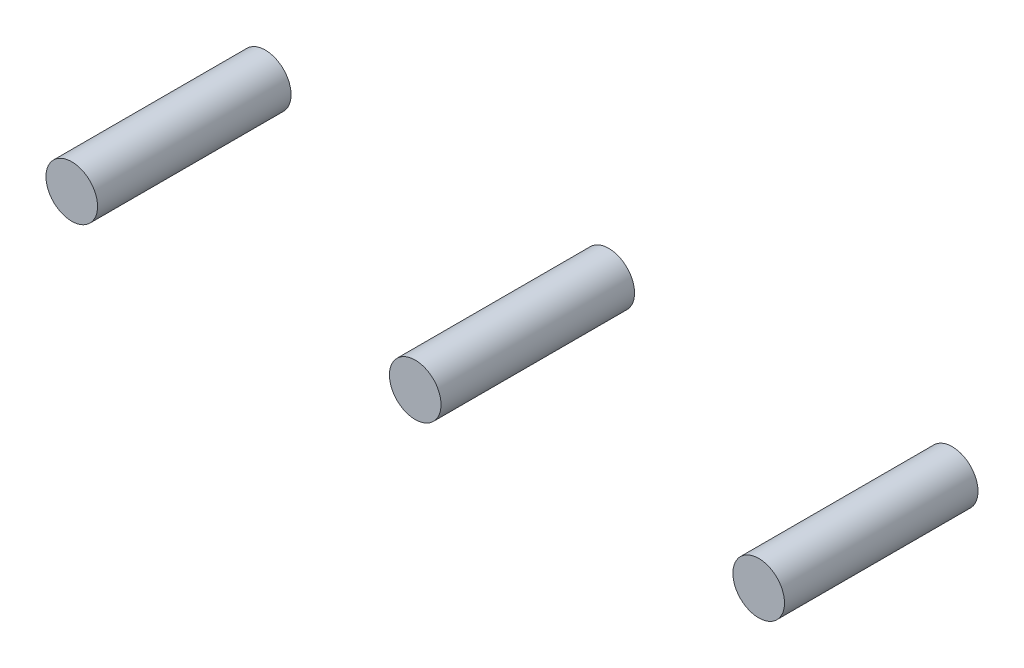
SolidWorks part; units mm, degrees
ref_plane "Front Plane" through (0, 0, 0) normal (0, 0, 1) x (1, 0, 0)
ref_plane "Top Plane" through (0, 0, 0) normal (0, 1, 0) x (1, 0, 0)
ref_plane "Right Plane" through (0, 0, 0) normal (1, 0, 0) x (0, 0, -1)
sketch "Sketch1" plane through (0, 0, 0) normal (0, 0, 1) x (1, 0, 0)
  line L0 (0, 5.75) -> (0, 0) construction
  line L1 (-1.6, 5.75) -> (1.6, 5.75) construction
  line L2 (1.6, 0) -> (-1.6, 0) construction
  line L3 (-6.325, 0) -> (-6.325, 5.75) construction
  line L4 (6.325, 0) -> (6.325, 5.75) construction
  circle A0 centre (0, 2.875) radius 0.4
  circle A1 centre (-5.325, 2.875) radius 0.4
  circle A2 centre (5.325, 2.875) radius 0.4
  dimension "D1" = 0.8
  dimension "D2" = 1
  dimension "D3" = 1
extrude "Extrude1" add sketch "Sketch1" along normal blind 3
